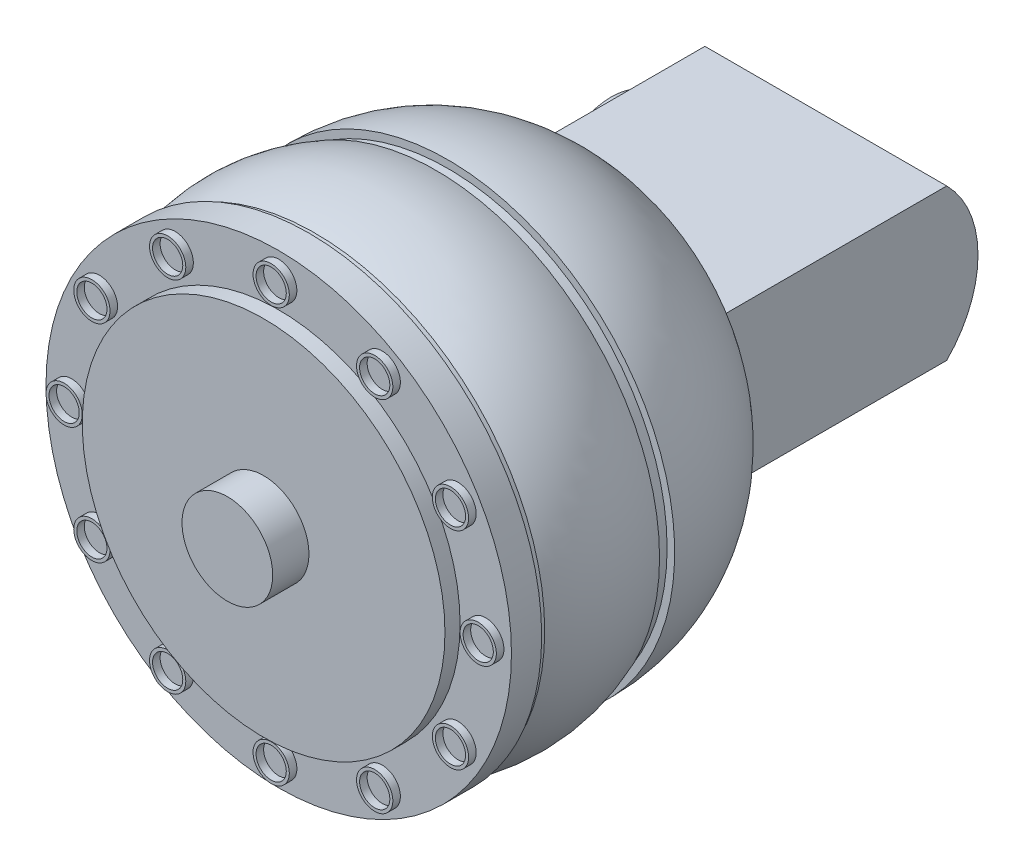
SolidWorks part; units mm, degrees
ref_plane "Front Plane" through (0, 0, 0) normal (0, 0, 1) x (1, 0, 0)
ref_plane "Top Plane" through (0, 0, 0) normal (0, 1, 0) x (1, 0, 0)
ref_plane "Right Plane" through (0, 0, 0) normal (1, 0, 0) x (0, 0, -1)
sketch "Sketch1" plane through (0, 0, 0) normal (0, 1, 0) x (1, 0, 0)
  line L0 (0, 0) -> (0, -12.7)
  line L1 (0, -12.7) -> (-19.05, -12.7)
  line L3 (-12.7, 0) -> (0, 0)
  arc A2 (-12.7, 0) -> (-19.05, -12.7) centre (-3.4964, -12.5393) ccw
  dimension "D1" = 12.7
  dimension "D2" = 12.7
  dimension "D3" = 19.05
sketch "Sketch2" plane through (0, 0, 0) normal (0, 1, 0) x (1, 0, 0)
revolve "Revolve3" add sketch "Sketch1" angle 360 about L0
sketch "Sketch3" plane through (0, 0, 12.7) normal (0, 0, 1) x (1, 0, 0)
  circle A0 centre (0, 0) radius 18.415
  dimension "D1" = 36.83
extrude "Boss-Extrude1" add sketch "Sketch3" along normal blind 1.016
sketch "Sketch4" plane through (0, 0, 0) normal (0, 1, 0) x (1, 0, 0)
  line L0 (0, -13.716) -> (-18.796, -13.716)
  line L1 (-18.415, -13.716) -> (18.415, -13.716) construction
  line L3 (-18.796, -23.876) -> (0, -23.876)
  line L4 (0, -23.876) -> (0, -13.716)
  arc A1 (-18.796, -13.716) -> (-18.796, -23.876) centre (-6.1897, -18.796) ccw
  dimension "D1" = 10.16
  dimension "D2" = 18.796
  dimension "D3" = 18.796
revolve "Revolve4" add sketch "Sketch4" angle 360 about L4
sketch "Sketch5" plane through (0, 0, 23.876) normal (0, 0, 1) x (1, 0, 0)
  circle A0 centre (0, 0) radius 19.304
  dimension "D1" = 38.608
extrude "Boss-Extrude2" add sketch "Sketch5" along normal blind 0.508
sketch "Sketch6" plane through (0, 0, 24.384) normal (0, 0, 1) x (1, 0, 0)
  circle A0 centre (0, 0) radius 19.558
  dimension "D1" = 39.116
extrude "Boss-Extrude3" add sketch "Sketch6" along normal blind 2.54
sketch "Sketch7" plane through (0, 0, 26.924) normal (0, 0, 1) x (1, 0, 0)
  circle A0 centre (0, 0) radius 15.24
  dimension "D1" = 30.48
extrude "Boss-Extrude4" add sketch "Sketch7" along normal blind 1.27
sketch "Sketch8" plane through (0, 0, 26.924) normal (0, 0, 1) x (1, 0, 0)
  circle A3 centre (17.399, 0) radius 1.524
  circle A4 centre (17.399, 0) radius 1.27
  dimension "D1" = 3.048
  dimension "D2" = 2.54
extrude "Boss-Extrude5" add sketch "Sketch8" along normal blind 0.635
pattern_circular "CirPattern1" count 12 over 360 about axis through (0, 0, 0) along (0, 0, 1) of "Boss-Extrude5"
sketch "Sketch9" plane through (0, 0, 0) normal (0, 0, -1) x (-1, 0, 0)
  line L1 (10.16, 6.35) -> (-10.16, 6.35)
  line L2 (10.16, 6.35) -> (10.16, -6.35)
  line L3 (10.16, -6.35) -> (-10.16, -6.35)
  line L4 (-10.16, 6.35) -> (-10.16, -6.35)
  line L5 (10.16, 6.35) -> (-10.16, -6.35) construction
  line L6 (10.16, -6.35) -> (-10.16, 6.35) construction
  point P0 (0, 0)
  dimension "D1" = 20.32
  dimension "D2" = 12.7
extrude "Boss-Extrude6" add sketch "Sketch9" along normal blind 19.05
sketch "Sketch10" plane through (10.16, 0, 0) normal (1, 0, 0) x (0, 0, -1)
  line L0 (19.05, 6.35) -> (19.05, -6.35)
  arc A0 (19.05, 6.35) -> (19.05, -6.35) centre (12.7, 0) cw
extrude "Boss-Extrude7" add sketch "Sketch10" against normal blind 20.32
sketch "Sketch12" plane through (0, 0, 28.194) normal (0, 0, 1) x (1, 0, 0)
  circle A0 centre (0, 0) radius 3.81
  dimension "D1" = 7.62
extrude "Boss-Extrude8" add sketch "Sketch12" along normal blind 3.048
sketch "Sketch13" plane through (-10.16, 0, 0) normal (-1, 0, 0) x (0, 0, 1)
  circle A0 centre (-12.7, 0) radius 5.08
  arc A1 (-19.05, 6.35) -> (-19.05, -6.35) centre (-12.7, 0) ccw construction
  dimension "0.4" = 10.16
extrude "Boss-Extrude9" add sketch "Sketch13" along normal blind 1.524
